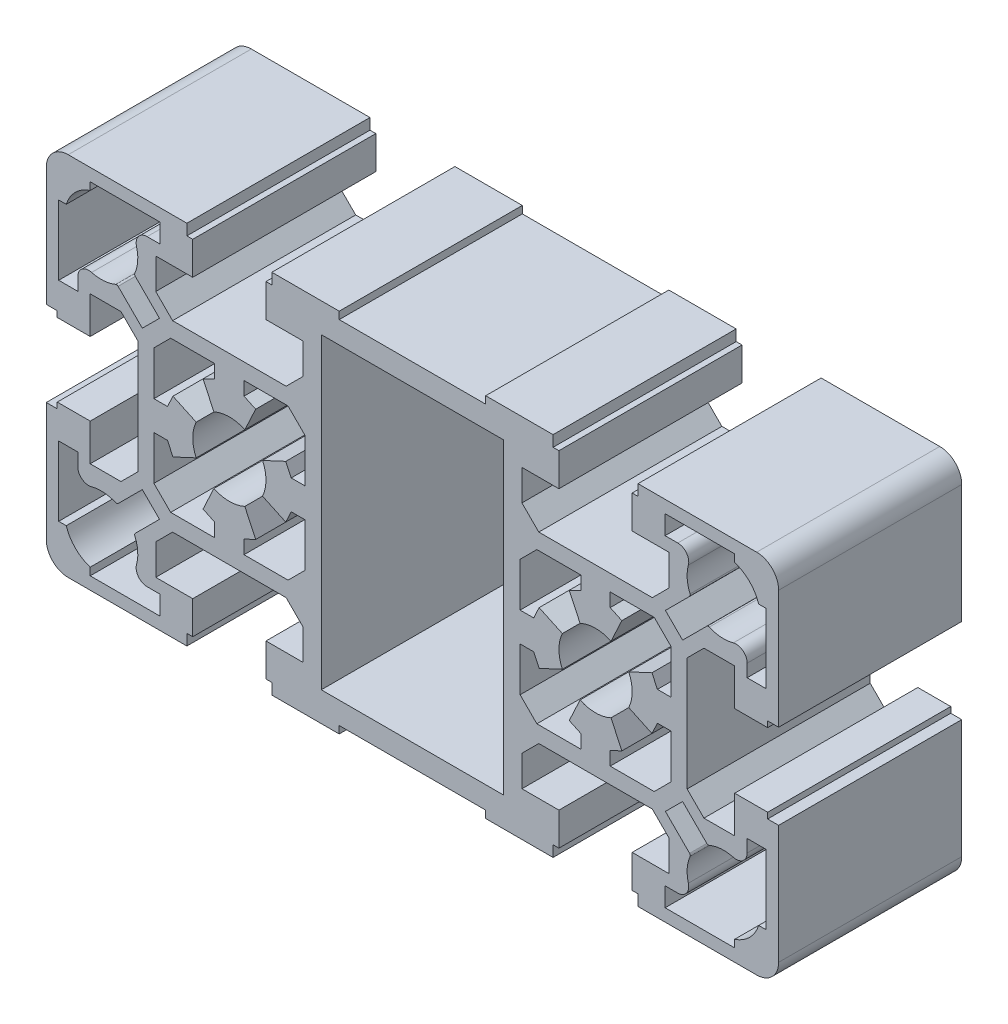
SolidWorks part; units mm, degrees
material "1060 Alloy"
ref_plane "Front" through (0, 0, 0) normal (0, 0, 1) x (1, 0, 0)
ref_plane "Top" through (0, 0, 0) normal (0, 1, 0) x (1, 0, 0)
ref_plane "Right" through (0, 0, 0) normal (1, 0, 0) x (0, 0, -1)
ref_plane "Plane1" through (0, 0, 0) normal (0, 0, -1) x (-1, 0, 0)
sketch "Sketch1" plane through (0, 0, 0) normal (0, 0, -1) x (-1, 0, 0)
  line L0 (37.8447, -15.1906) -> (34.5389, -11.8847)
  line L1 (34.5389, -11.8847) -> (36.8847, -9.5389)
  line L2 (36.8847, -9.5389) -> (40.1906, -12.8447)
  line L3 (45.7, -11.2262) -> (45.7, -9.5)
  line L4 (45.7, -9.5) -> (48.3, -9.5)
  line L5 (48.3, -9.5) -> (48.3, -19)
  line L6 (48.3, -19) -> (47.2697, -19)
  line L7 (44, -22.2697) -> (44, -23.3)
  line L8 (44, -23.3) -> (34.5, -23.3)
  line L9 (34.5, -23.3) -> (34.5, -20.7)
  line L10 (34.5, -20.7) -> (36.2262, -20.7)
  line L11 (-40.1906, -12.8447) -> (-36.8847, -9.5389)
  line L12 (-36.8847, -9.5389) -> (-34.5389, -11.8847)
  line L13 (-34.5389, -11.8847) -> (-37.8447, -15.1906)
  line L14 (-36.2262, -20.7) -> (-34.5, -20.7)
  line L15 (-34.5, -20.7) -> (-34.5, -23.3)
  line L16 (-34.5, -23.3) -> (-44, -23.3)
  line L17 (-44, -23.3) -> (-44, -22.2697)
  line L18 (-47.2697, -19) -> (-48.3, -19)
  line L19 (-48.3, -19) -> (-48.3, -9.5)
  line L20 (-48.3, -9.5) -> (-45.7, -9.5)
  line L21 (-45.7, -9.5) -> (-45.7, -11.2262)
  line L22 (48.3, 19) -> (48.3, 9.5)
  line L23 (48.3, 9.5) -> (45.7, 9.5)
  line L24 (45.7, 9.5) -> (45.7, 11.2262)
  line L25 (40.1906, 12.8447) -> (36.8847, 9.5389)
  line L26 (36.8847, 9.5389) -> (34.5389, 11.8847)
  line L27 (34.5389, 11.8847) -> (37.8447, 15.1906)
  line L28 (36.2262, 20.7) -> (34.5, 20.7)
  line L29 (34.5, 20.7) -> (34.5, 23.3)
  line L30 (34.5, 23.3) -> (44, 23.3)
  line L31 (44, 23.3) -> (44, 22.2697)
  line L32 (47.2697, 19) -> (48.3, 19)
  line L33 (-34.5, 23.3) -> (-34.5, 20.7)
  line L34 (-34.5, 20.7) -> (-36.2262, 20.7)
  line L35 (-37.8447, 15.1906) -> (-34.5389, 11.8847)
  line L36 (-34.5389, 11.8847) -> (-36.8847, 9.5389)
  line L37 (-36.8847, 9.5389) -> (-40.1906, 12.8447)
  line L38 (-45.7, 11.2262) -> (-45.7, 9.5)
  line L39 (-45.7, 9.5) -> (-48.3, 9.5)
  line L40 (-48.3, 9.5) -> (-48.3, 19)
  line L41 (-48.3, 19) -> (-47.2697, 19)
  line L42 (-44, 22.2697) -> (-44, 23.3)
  line L43 (-44, 23.3) -> (-34.5, 23.3)
  line L44 (-23, 10.3) -> (-16.9877, 10.3)
  line L45 (-16.9877, 10.3) -> (-14.7, 8.0123)
  line L46 (-14.7, 8.0123) -> (-14.7, 2)
  line L47 (-14.7, 2) -> (-16.5539, 2)
  line L48 (-16.5539, 2) -> (-17.2964, 3.5923)
  line L49 (-17.2964, 3.5923) -> (-20.4685, 2.1131)
  line L50 (-20.4685, -2.1131) -> (-17.2964, -3.5923)
  line L51 (-17.2964, -3.5923) -> (-16.5539, -2)
  line L52 (-16.5539, -2) -> (-14.7, -2)
  line L53 (-14.7, -2) -> (-14.7, -8.0123)
  line L54 (-14.7, -8.0123) -> (-16.9877, -10.3)
  line L55 (-16.9877, -10.3) -> (-23, -10.3)
  line L56 (-23, -10.3) -> (-23, -8.4461)
  line L57 (-23, -8.4461) -> (-21.4077, -7.7036)
  line L58 (-21.4077, -7.7036) -> (-22.8869, -4.5315)
  line L59 (-27.1131, -4.5315) -> (-28.5923, -7.7036)
  line L60 (-28.5923, -7.7036) -> (-27, -8.4461)
  line L61 (-27, -8.4461) -> (-27, -10.3)
  line L62 (-27, -10.3) -> (-33.0123, -10.3)
  line L63 (-33.0123, -10.3) -> (-35.3, -8.0123)
  line L64 (-35.3, -8.0123) -> (-35.3, -2)
  line L65 (-35.3, -2) -> (-33.4461, -2)
  line L66 (-33.4461, -2) -> (-32.7036, -3.5923)
  line L67 (-32.7036, -3.5923) -> (-29.5315, -2.1131)
  line L68 (-29.5315, 2.1131) -> (-32.7036, 3.5923)
  line L69 (-32.7036, 3.5923) -> (-33.4461, 2)
  line L70 (-33.4461, 2) -> (-35.3, 2)
  line L71 (-35.3, 2) -> (-35.3, 8.0123)
  line L72 (-35.3, 8.0123) -> (-33.0123, 10.3)
  line L73 (-33.0123, 10.3) -> (-27, 10.3)
  line L74 (-27, 10.3) -> (-27, 8.4461)
  line L75 (-27, 8.4461) -> (-28.5923, 7.7036)
  line L76 (-28.5923, 7.7036) -> (-27.1131, 4.5315)
  line L77 (-22.8869, 4.5315) -> (-21.4077, 7.7036)
  line L78 (-21.4077, 7.7036) -> (-23, 8.4461)
  line L79 (-23, 8.4461) -> (-23, 10.3)
  line L80 (35.3, -8.0123) -> (33.0123, -10.3)
  line L81 (33.0123, -10.3) -> (27, -10.3)
  line L82 (27, -10.3) -> (27, -8.4461)
  line L83 (27, -8.4461) -> (28.5923, -7.7036)
  line L84 (28.5923, -7.7036) -> (27.1131, -4.5315)
  line L85 (22.8869, -4.5315) -> (21.4077, -7.7036)
  line L86 (21.4077, -7.7036) -> (23, -8.4461)
  line L87 (23, -8.4461) -> (23, -10.3)
  line L88 (23, -10.3) -> (16.9877, -10.3)
  line L89 (16.9877, -10.3) -> (14.7, -8.0123)
  line L90 (14.7, -8.0123) -> (14.7, -2)
  line L91 (14.7, -2) -> (16.5539, -2)
  line L92 (16.5539, -2) -> (17.2964, -3.5923)
  line L93 (17.2964, -3.5923) -> (20.4685, -2.1131)
  line L94 (20.4685, 2.1131) -> (17.2964, 3.5923)
  line L95 (17.2964, 3.5923) -> (16.5539, 2)
  line L96 (16.5539, 2) -> (14.7, 2)
  line L97 (14.7, 2) -> (14.7, 8.0123)
  line L98 (14.7, 8.0123) -> (16.9877, 10.3)
  line L99 (16.9877, 10.3) -> (23, 10.3)
  line L100 (23, 10.3) -> (23, 8.4461)
  line L101 (23, 8.4461) -> (21.4077, 7.7036)
  line L102 (21.4077, 7.7036) -> (22.8869, 4.5315)
  line L103 (27.1131, 4.5315) -> (28.5923, 7.7036)
  line L104 (28.5923, 7.7036) -> (27, 8.4461)
  line L105 (27, 8.4461) -> (27, 10.3)
  line L106 (27, 10.3) -> (33.0123, 10.3)
  line L107 (33.0123, 10.3) -> (35.3, 8.0123)
  line L108 (35.3, 8.0123) -> (35.3, 2)
  line L109 (35.3, 2) -> (33.4461, 2)
  line L110 (33.4461, 2) -> (32.7036, 3.5923)
  line L111 (32.7036, 3.5923) -> (29.5315, 2.1131)
  line L112 (29.5315, -2.1131) -> (32.7036, -3.5923)
  line L113 (32.7036, -3.5923) -> (33.4461, -2)
  line L114 (33.4461, -2) -> (35.3, -2)
  line L115 (35.3, -2) -> (35.3, -8.0123)
  line L116 (12.45, -21) -> (-12.45, -21)
  line L117 (-12.45, -21) -> (-12.45, 21)
  line L118 (-12.45, 21) -> (12.45, 21)
  line L119 (12.45, 21) -> (12.45, -21)
  line L120 (-30, -23.5) -> (-30, -19)
  line L121 (-30, -19) -> (-35.05, -19)
  line L122 (-35.05, -19) -> (-35.05, -14.8)
  line L123 (-35.05, -14.8) -> (-32.75, -12.5)
  line L124 (-32.75, -12.5) -> (-17.25, -12.5)
  line L125 (-17.25, -12.5) -> (-14.95, -14.8)
  line L126 (-14.95, -14.8) -> (-14.95, -19)
  line L127 (-14.95, -19) -> (-20, -19)
  line L128 (-20, -19) -> (-20, -23.5)
  line L129 (-20, -23.5) -> (-19.2, -23.5)
  line L130 (-19.2, -23.5) -> (-19.2, -25)
  line L131 (-19.2, -25) -> (-10, -25)
  line L132 (-10, -25) -> (-10, -24)
  line L133 (-10, -24) -> (10, -24)
  line L134 (10, -24) -> (10, -25)
  line L135 (10, -25) -> (19.2, -25)
  line L136 (19.2, -25) -> (19.2, -23.5)
  line L137 (19.2, -23.5) -> (20, -23.5)
  line L138 (20, -23.5) -> (20, -19)
  line L139 (20, -19) -> (14.95, -19)
  line L140 (14.95, -19) -> (14.95, -14.8)
  line L141 (14.95, -14.8) -> (17.25, -12.5)
  line L142 (17.25, -12.5) -> (32.75, -12.5)
  line L143 (32.75, -12.5) -> (35.05, -14.8)
  line L144 (35.05, -14.8) -> (35.05, -19)
  line L145 (35.05, -19) -> (30, -19)
  line L146 (30, -19) -> (30, -23.5)
  line L147 (30, -23.5) -> (30.8, -23.5)
  line L148 (30.8, -23.5) -> (30.8, -25)
  line L149 (30.8, -25) -> (47, -25)
  line L150 (50, -22) -> (50, -5.8)
  line L151 (50, -5.8) -> (48.5, -5.8)
  line L152 (48.5, -5.8) -> (48.5, -5)
  line L153 (48.5, -5) -> (44, -5)
  line L154 (44, -5) -> (44, -10.05)
  line L155 (44, -10.05) -> (39.8, -10.05)
  line L156 (39.8, -10.05) -> (37.5, -7.75)
  line L157 (37.5, -7.75) -> (37.5, 7.75)
  line L158 (37.5, 7.75) -> (39.8, 10.05)
  line L159 (39.8, 10.05) -> (44, 10.05)
  line L160 (44, 10.05) -> (44, 5)
  line L161 (44, 5) -> (48.5, 5)
  line L162 (48.5, 5) -> (48.5, 5.8)
  line L163 (48.5, 5.8) -> (50, 5.8)
  line L164 (50, 5.8) -> (50, 22)
  line L165 (47, 25) -> (30.8, 25)
  line L166 (30.8, 25) -> (30.8, 23.5)
  line L167 (30.8, 23.5) -> (30, 23.5)
  line L168 (30, 23.5) -> (30, 19)
  line L169 (30, 19) -> (35.05, 19)
  line L170 (35.05, 19) -> (35.05, 14.8)
  line L171 (35.05, 14.8) -> (32.75, 12.5)
  line L172 (32.75, 12.5) -> (17.25, 12.5)
  line L173 (17.25, 12.5) -> (14.95, 14.8)
  line L174 (14.95, 14.8) -> (14.95, 19)
  line L175 (14.95, 19) -> (20, 19)
  line L176 (20, 19) -> (20, 23.5)
  line L177 (20, 23.5) -> (19.2, 23.5)
  line L178 (19.2, 23.5) -> (19.2, 25)
  line L179 (19.2, 25) -> (10, 25)
  line L180 (10, 25) -> (10, 24)
  line L181 (10, 24) -> (-10, 24)
  line L182 (-10, 24) -> (-10, 25)
  line L183 (-10, 25) -> (-19.2, 25)
  line L184 (-19.2, 25) -> (-19.2, 23.5)
  line L185 (-19.2, 23.5) -> (-20, 23.5)
  line L186 (-20, 23.5) -> (-20, 19)
  line L187 (-20, 19) -> (-14.95, 19)
  line L188 (-14.95, 19) -> (-14.95, 14.8)
  line L189 (-14.95, 14.8) -> (-17.25, 12.5)
  line L190 (-17.25, 12.5) -> (-32.75, 12.5)
  line L191 (-32.75, 12.5) -> (-35.05, 14.8)
  line L192 (-35.05, 14.8) -> (-35.05, 19)
  line L193 (-35.05, 19) -> (-30, 19)
  line L194 (-30, 19) -> (-30, 23.5)
  line L195 (-30, 23.5) -> (-30.8, 23.5)
  line L196 (-30.8, 23.5) -> (-30.8, 25)
  line L197 (-30.8, 25) -> (-47, 25)
  line L198 (-50, 22) -> (-50, 5.8)
  line L199 (-50, 5.8) -> (-48.5, 5.8)
  line L200 (-48.5, 5.8) -> (-48.5, 5)
  line L201 (-48.5, 5) -> (-44, 5)
  line L202 (-44, 5) -> (-44, 10.05)
  line L203 (-44, 10.05) -> (-39.8, 10.05)
  line L204 (-39.8, 10.05) -> (-37.5, 7.75)
  line L205 (-37.5, 7.75) -> (-37.5, -7.75)
  line L206 (-37.5, -7.75) -> (-39.8, -10.05)
  line L207 (-39.8, -10.05) -> (-44, -10.05)
  line L208 (-44, -10.05) -> (-44, -5)
  line L209 (-44, -5) -> (-48.5, -5)
  line L210 (-48.5, -5) -> (-48.5, -5.8)
  line L211 (-48.5, -5.8) -> (-50, -5.8)
  line L212 (-50, -5.8) -> (-50, -22)
  line L213 (-47, -25) -> (-30.8, -25)
  line L214 (-30.8, -25) -> (-30.8, -23.5)
  line L215 (-30.8, -23.5) -> (-30, -23.5)
  arc A0 (37.9081, -15.5214) -> (37.8447, -15.1906) centre (37.6326, -15.4027) ccw
  arc A1 (40.1906, -12.8447) -> (40.5214, -12.9081) centre (40.4027, -12.6326) ccw
  arc A2 (40.5214, -12.9081) -> (43.8077, -12.674) centre (42.5, -17.5) cw
  arc A3 (43.8077, -12.674) -> (45.7, -11.2262) centre (44.2, -11.2262) ccw
  arc A4 (47.2697, -19) -> (44, -22.2697) centre (42.5, -17.5) cw
  arc A5 (36.2262, -20.7) -> (37.674, -18.8077) centre (36.2262, -19.2) ccw
  arc A6 (37.674, -18.8077) -> (37.9081, -15.5214) centre (42.5, -17.5) cw
  arc A7 (-37.8447, -15.1906) -> (-37.9081, -15.5214) centre (-37.6326, -15.4027) ccw
  arc A8 (-37.9081, -15.5214) -> (-37.674, -18.8077) centre (-42.5, -17.5) cw
  arc A9 (-37.674, -18.8077) -> (-36.2262, -20.7) centre (-36.2262, -19.2) ccw
  arc A10 (-44, -22.2697) -> (-47.2697, -19) centre (-42.5, -17.5) cw
  arc A11 (-45.7, -11.2262) -> (-43.8077, -12.674) centre (-44.2, -11.2262) ccw
  arc A12 (-43.8077, -12.674) -> (-40.5214, -12.9081) centre (-42.5, -17.5) cw
  arc A13 (-40.5214, -12.9081) -> (-40.1906, -12.8447) centre (-40.4027, -12.6326) ccw
  arc A14 (45.7, 11.2262) -> (43.8077, 12.674) centre (44.2, 11.2262) ccw
  arc A15 (43.8077, 12.674) -> (40.5214, 12.9081) centre (42.5, 17.5) cw
  arc A16 (40.5214, 12.9081) -> (40.1906, 12.8447) centre (40.4027, 12.6326) ccw
  arc A17 (37.8447, 15.1906) -> (37.9081, 15.5214) centre (37.6326, 15.4027) ccw
  arc A18 (37.9081, 15.5214) -> (37.674, 18.8077) centre (42.5, 17.5) cw
  arc A19 (37.674, 18.8077) -> (36.2262, 20.7) centre (36.2262, 19.2) ccw
  arc A20 (44, 22.2697) -> (47.2697, 19) centre (42.5, 17.5) cw
  arc A21 (-36.2262, 20.7) -> (-37.674, 18.8077) centre (-36.2262, 19.2) ccw
  arc A22 (-37.674, 18.8077) -> (-37.9081, 15.5214) centre (-42.5, 17.5) cw
  arc A23 (-37.9081, 15.5214) -> (-37.8447, 15.1906) centre (-37.6326, 15.4027) ccw
  arc A24 (-40.1906, 12.8447) -> (-40.5214, 12.9081) centre (-40.4027, 12.6326) ccw
  arc A25 (-40.5214, 12.9081) -> (-43.8077, 12.674) centre (-42.5, 17.5) cw
  arc A26 (-43.8077, 12.674) -> (-45.7, 11.2262) centre (-44.2, 11.2262) ccw
  arc A27 (-47.2697, 19) -> (-44, 22.2697) centre (-42.5, 17.5) cw
  arc A28 (-20.4685, 2.1131) -> (-20.4685, -2.1131) centre (-25, 0) cw
  arc A29 (-22.8869, -4.5315) -> (-27.1131, -4.5315) centre (-25, 0) cw
  arc A30 (-29.5315, -2.1131) -> (-29.5315, 2.1131) centre (-25, 0) cw
  arc A31 (-27.1131, 4.5315) -> (-22.8869, 4.5315) centre (-25, 0) cw
  arc A32 (27.1131, -4.5315) -> (22.8869, -4.5315) centre (25, 0) cw
  arc A33 (20.4685, -2.1131) -> (20.4685, 2.1131) centre (25, 0) cw
  arc A34 (22.8869, 4.5315) -> (27.1131, 4.5315) centre (25, 0) cw
  arc A35 (29.5315, 2.1131) -> (29.5315, -2.1131) centre (25, 0) cw
  arc A36 (47, -25) -> (50, -22) centre (47, -22) ccw
  arc A37 (50, 22) -> (47, 25) centre (47, 22) ccw
  arc A38 (-47, 25) -> (-50, 22) centre (-47, 22) ccw
  arc A39 (-50, -22) -> (-47, -25) centre (-47, -22) ccw
extrude "Boss-Extrude1" add sketch "Sketch1" against normal blind 25
